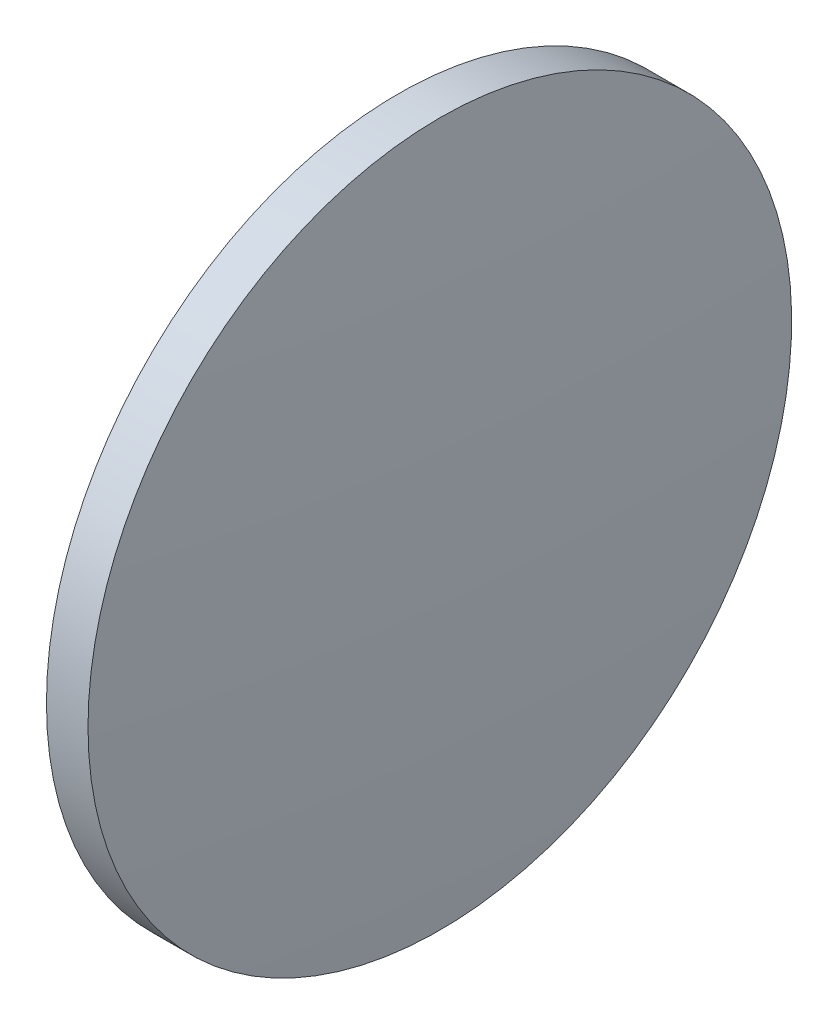
SolidWorks part; units mm, degrees
ref_plane "前视基准面" through (0, 0, 0) normal (0, 0, 1) x (1, 0, 0)
ref_plane "上视基准面" through (0, 0, 0) normal (0, 1, 0) x (1, 0, 0)
ref_plane "右视基准面" through (0, 0, 0) normal (1, 0, 0) x (0, 0, -1)
sketch "草图1" plane through (0, 0, 0) normal (0, 0, 1) x (1, 0, 0)
  line L0 (220.3307, 130.4671) -> (257.9227, 130.4671) construction
  line L1 (232.0208, 130.4671) -> (232.0208, 155.8671)
  line L2 (232.0208, 155.8671) -> (235.0208, 155.8671)
  line L3 (235.9208, 130.4671) -> (232.0208, 130.4671)
  arc A0 (235.9208, 130.4671) -> (235.0208, 155.8671) centre (-122.9514, 130.4671) ccw
revolve "旋转1" add sketch "草图1" angle 360 about L0
